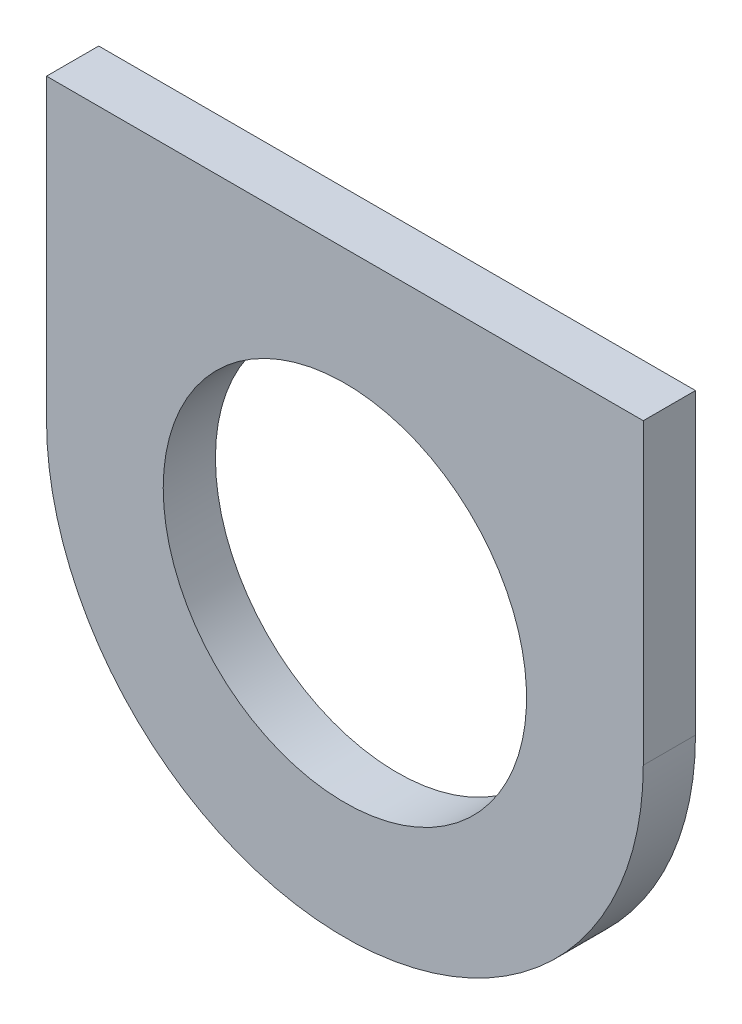
SolidWorks part; units mm, degrees
material "Polyetheretherketone (PEEK)"
ref_plane "Front Plane" through (0, 0, 0) normal (0, 0, 1) x (1, 0, 0)
ref_plane "Top Plane" through (0, 0, 0) normal (0, 1, 0) x (1, 0, 0)
ref_plane "Right Plane" through (0, 0, 0) normal (1, 0, 0) x (0, 0, -1)
sketch "Sketch1" plane through (0, 0, 764.1674) normal (0, 0, -1) x (-1, 0, 0)
  line L0 (108.2044, 637.4686) -> (108.2044, 640.3261)
  line L1 (111.0619, 640.3261) -> (108.2044, 640.3261)
  line L2 (111.0619, 640.3261) -> (113.9194, 640.3261)
  line L3 (113.9194, 637.4686) -> (113.9194, 640.3261)
  arc A0 (108.2044, 637.4686) -> (113.9194, 637.4686) centre (111.0619, 637.4686) ccw
  circle A1 centre (111.0619, 637.4686) radius 2.8575 construction
  circle A2 centre (111.0619, 637.4686) radius 1.7399
extrude "Boss-Extrude1" add sketch "Sketch1" along normal blind 0.5
